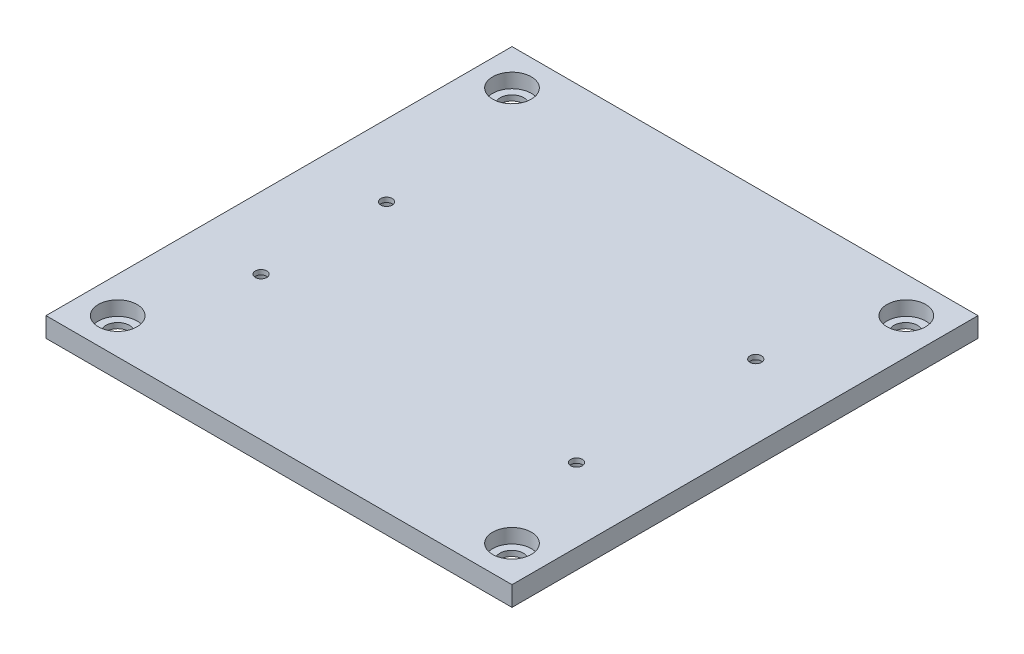
SolidWorks part; units mm, degrees
ref_plane "前视基准面" through (0, 0, 0) normal (0, 0, 1) x (1, 0, 0)
ref_plane "上视基准面" through (0, 0, 0) normal (0, 1, 0) x (1, 0, 0)
ref_plane "右视基准面" through (0, 0, 0) normal (1, 0, 0) x (0, 0, -1)
sketch "草图1" plane through (0, 0, 0) normal (0, 1, 0) x (1, 0, 0)
  line L1 (0, 0) -> (130, 0)
  line L2 (0, 0) -> (0, 130)
  line L3 (0, 130) -> (130, 130)
  line L4 (130, 0) -> (130, 130)
  dimension "D1" = 130
  dimension "D2" = 130
extrude "凸台-拉伸1" add sketch "草图1" along normal blind 5.5
sketch "草图4" plane through (0, 5.5, 0) normal (0, 1, 0) x (1, 0, 0)
  line L1 (0, 0) -> (130, 0) construction
  line L2 (130, 0) -> (130, 130) construction
  line L4 (130, 130) -> (0, 130) construction
  circle A0 centre (10, 120) radius 5.4
  circle A1 centre (120, 120) radius 5.4
  circle A2 centre (10, 10) radius 5.4
  circle A3 centre (120, 10) radius 5.4
  dimension "D1" = 110
  dimension "D2" = 10.8
  dimension "D4" = 10.8
  dimension "D6" = 10.8
  dimension "D7" = 10
  dimension "D10" = 10.8
  dimension "D3" = 110
  dimension "D5" = 10
  dimension "D8" = 10
  dimension "D9" = 10
extrude "切除-拉伸7" cut sketch "草图4" against normal blind 4 contours A2 | A3 | A1 | A0
sketch "草图6" plane through (0, 1.5, 0) normal (0, 1, 0) x (1, 0, 0)
  circle A5 centre (10, 120) radius 3.3
  circle A6 centre (119.916, 119.916) radius 3.3
  circle A7 centre (10, 10) radius 3.3
  circle A8 centre (120, 9.916) radius 3.3
  dimension "D1" = 6.6
  dimension "D2" = 6.6
  dimension "D3" = 6.6
  dimension "D4" = 6.6
extrude "切除-拉伸8" cut sketch "草图6" against normal blind 1.5
sketch "草图7" plane through (0, 0, 0) normal (0, -1, 0) x (1, 0, 0)
  circle A0 centre (20, -40) radius 3.1
  circle A1 centre (20, -75) radius 3.1
  circle A2 centre (109.5, -38.5) radius 3.1
  circle A3 centre (109.5, -88.5) radius 3.1
  dimension "D1" = 6.2
  dimension "D2" = 6.2
  dimension "D3" = 6.2
  dimension "D4" = 6.2
  dimension "D5" = 35
  dimension "D6" = 50
extrude "切除-拉伸9" cut sketch "草图7" against normal blind 4.2
sketch "草图8" plane through (0, 4.2, 0) normal (0, -1, 0) x (1, 0, 0)
  circle A0 centre (20, -40) radius 1.6
  circle A1 centre (20, -75) radius 1.6
  circle A4 centre (109.5, -38.5) radius 1.6
  circle A5 centre (109.5, -88.5) radius 1.6
  dimension "D1" = 3.2
  dimension "D2" = 3.2
  dimension "D3" = 3.2
  dimension "D4" = 3.2
extrude "切除-拉伸10" cut sketch "草图8" against normal through all
